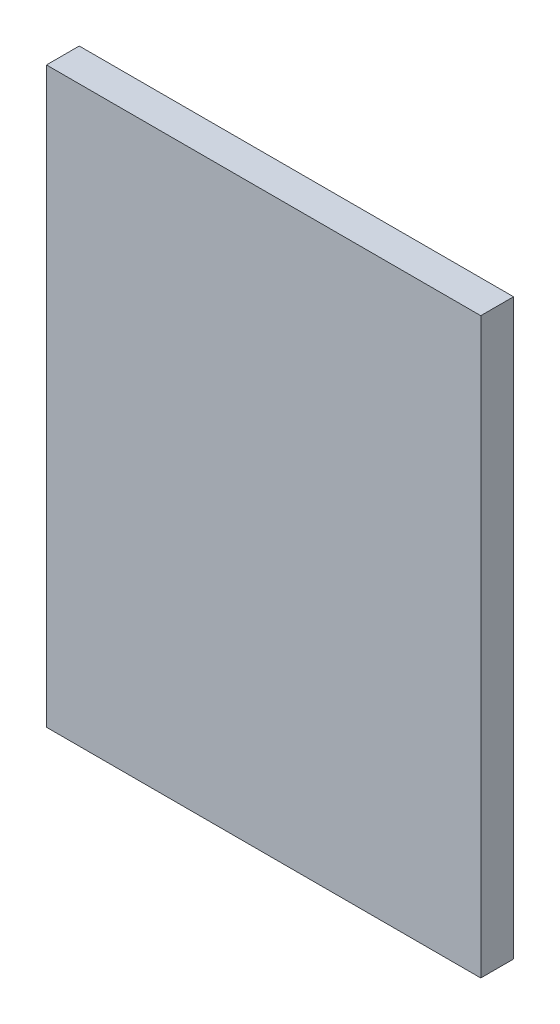
SolidWorks part; units mm, degrees
ref_plane "Front Plane" through (0, 0, 0) normal (0, 0, 1) x (1, 0, 0)
ref_plane "Top Plane" through (0, 0, 0) normal (0, 1, 0) x (1, 0, 0)
ref_plane "Right Plane" through (0, 0, 0) normal (1, 0, 0) x (0, 0, -1)
sketch "Sketch1" plane through (0, 0, 0) normal (0, 0, 1) x (1, 0, 0)
  line L1 (-13.25, 17.5) -> (13.25, 17.5)
  line L2 (-13.25, 17.5) -> (-13.25, -17.5)
  line L3 (-13.25, -17.5) -> (13.25, -17.5)
  line L4 (13.25, 17.5) -> (13.25, -17.5)
  line L5 (-13.25, 17.5) -> (13.25, -17.5) construction
  line L6 (-13.25, -17.5) -> (13.25, 17.5) construction
  point P0 (0, 0)
  dimension "D1" = 35
  dimension "D2" = 26.5
extrude "Boss-Extrude1" add sketch "Sketch1" along normal blind 2
